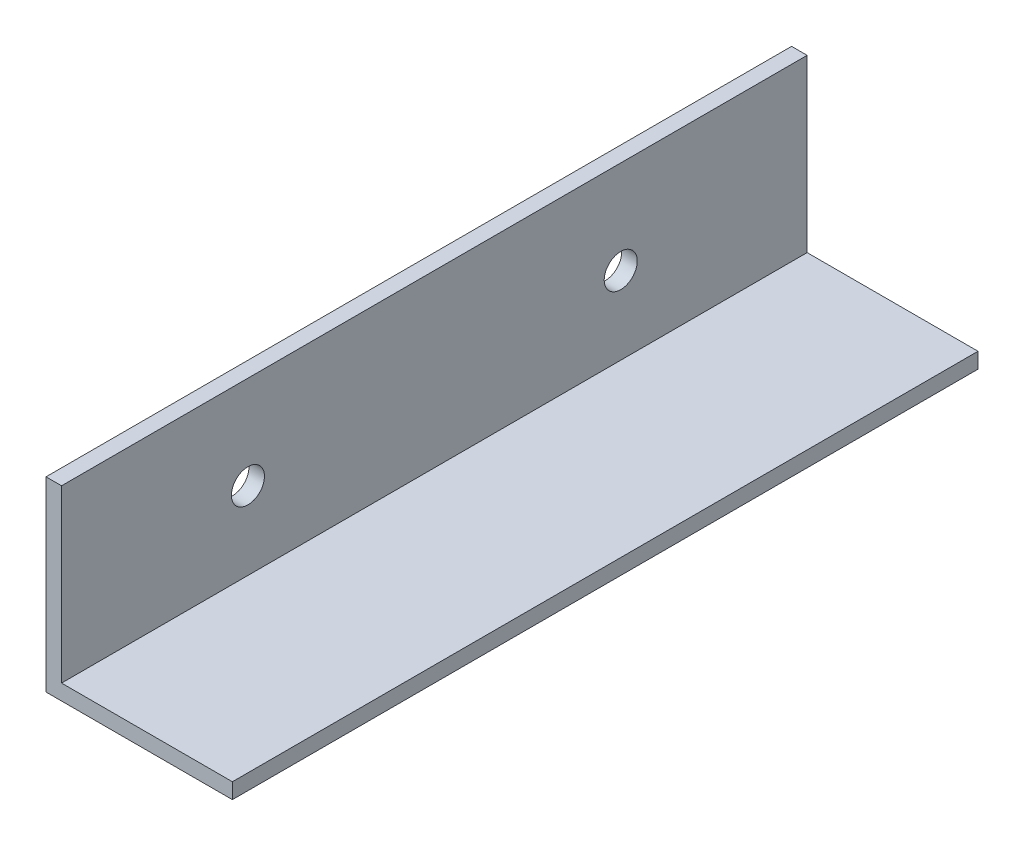
SolidWorks part; units mm, degrees
material "6061 Alloy"
ref_plane "Front Plane" through (0, 0, 0) normal (0, 0, 1) x (1, 0, 0)
ref_plane "Top Plane" through (0, 0, 0) normal (0, 1, 0) x (1, 0, 0)
ref_plane "Right Plane" through (0, 0, 0) normal (1, 0, 0) x (0, 0, -1)
sketch "Sketch1" plane through (0, 0, 0) normal (0, 0, 1) x (1, 0, 0)
  line L0 (0, 0) -> (0, 38.1)
  line L1 (0, 38.1) -> (3.175, 38.1)
  line L2 (3.175, 38.1) -> (3.175, 3.175)
  line L3 (3.175, 3.175) -> (38.1, 3.175)
  line L4 (38.1, 3.175) -> (38.1, 0)
  line L5 (38.1, 0) -> (0, 0)
  dimension "D1" = 38.1
  dimension "D2" = 3.175
extrude "Boss-Extrude1" add sketch "Sketch1" along normal blind 152.4
hole_wizard "1/4 Clearance Hole1" positions "Sketch2" profile "Sketch3" hole size "1/4" standard "ANSI Inch" end condition through all
sketch "Sketch2" plane through (0, 0, 0) normal (-1, 0, 0) x (0, 0, 1)
  line L0 (0, 38.1) -> (0, 0) construction
  line L1 (152.4, 38.1) -> (152.4, 0) construction
  line L2 (152.4, 0) -> (0, 0) construction
  point P0 (38.1, 19.05)
  point P2 (114.3, 19.05)
  dimension "D1" = 38.1
  dimension "D2" = 38.1
  dimension "D3" = 19.05
sketch "Sketch3" plane through (0, 19.05, 38.1) normal (0, 1, 0) x (0, 0, 1)
  line L0 (0, 0) -> (0, 38.1)
  line L1 (0, 38.1) -> (3.3782, 38.1)
  line L2 (3.3782, 38.1) -> (3.3782, 0)
  line L5 (3.3782, 0) -> (0, 0)
  line L11 (0, -6.35) -> (0, 107.95) construction
  dimension "Thru Hole Dia." = 6.7564
  dimension "Thru Hole Depth" = 38.1
